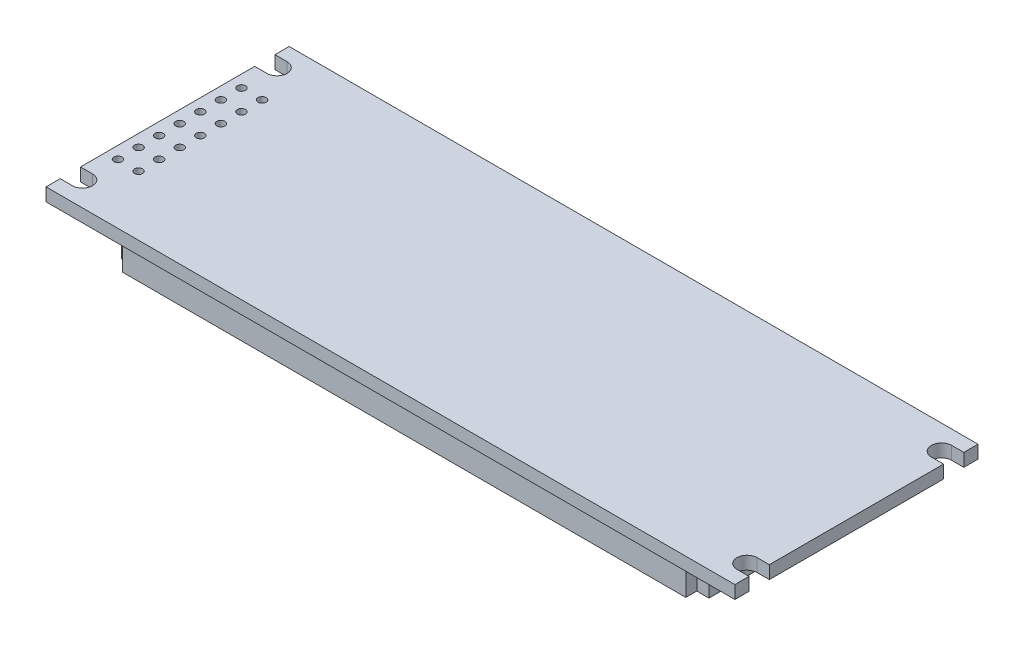
SolidWorks part; units mm, degrees
ref_plane "Plan de face" through (0, 0, 0) normal (0, 0, 1) x (1, 0, 0)
ref_plane "Plan de dessus" through (0, 0, 0) normal (0, 1, 0) x (1, 0, 0)
ref_plane "Plan de droite" through (0, 0, 0) normal (1, 0, 0) x (0, 0, -1)
sketch "Esquisse1" plane through (0, 0, 0) normal (0, 1, 0) x (1, 0, 0)
  line L0 (-41, -13.25) -> (-42.5, -13.25)
  line L1 (42.5, 15) -> (-42.5, 15)
  line L2 (-42.5, -10.75) -> (-42.5, 10.75)
  line L3 (42.5, -15) -> (-42.5, -15)
  line L4 (-42.5, -15) -> (-42.5, -13.25)
  line L5 (0, -15) -> (0, 15) construction
  line L6 (42.5, -15) -> (-42.5, 15) construction
  line L7 (-42.5, -10.75) -> (-41, -10.75)
  line L8 (-42.5, 0) -> (42.5, 0) construction
  line L10 (-42.5, 10.75) -> (-41, 10.75)
  line L11 (-42.5, 15) -> (-42.5, 13.25)
  line L12 (-41, 13.25) -> (-42.5, 13.25)
  line L13 (42.5, 15) -> (42.5, 13.25)
  line L14 (41, 13.25) -> (42.5, 13.25)
  line L15 (42.5, 10.75) -> (41, 10.75)
  line L16 (-42.5, 15) -> (42.5, -15) construction
  line L17 (42.5, -10.75) -> (41, -10.75)
  line L18 (42.5, -15) -> (42.5, -13.25)
  line L19 (41, -13.25) -> (42.5, -13.25)
  line L20 (42.5, -10.75) -> (42.5, 10.75)
  arc A0 (-41, -13.25) -> (-41, -10.75) centre (-41, -12) ccw
  arc A1 (-41, 13.25) -> (-41, 10.75) centre (-41, 12) cw
  arc A2 (41, 13.25) -> (41, 10.75) centre (41, 12) ccw
  arc A3 (41, -13.25) -> (41, -10.75) centre (41, -12) cw
  point P0 (0, 0)
  dimension "D1" = 85
  dimension "D3" = 82
  dimension "D5" = 1.25
  dimension "D2" = 30
  dimension "D4" = 24
extrude "Boss.-Extru.1" add sketch "Esquisse1" along normal blind 1.6
sketch "Esquisse2" plane through (0, 0, 0) normal (0, -1, 0) x (1, 0, 0)
  line L2 (42.5, 15) -> (-42.5, 15) construction
  line L3 (-42.5, 10.75) -> (-42.5, -10.75) construction
  circle A0 centre (-41, 7.62) radius 0.5
  circle A1 centre (-38.46, 7.62) radius 0.5
  circle A2 centre (-38.46, 5.08) radius 0.5
  circle A3 centre (-38.46, 2.54) radius 0.5
  circle A4 centre (-38.46, 0) radius 0.5
  circle A5 centre (-38.46, -2.54) radius 0.5
  circle A6 centre (-38.46, -5.08) radius 0.5
  circle A7 centre (-38.46, -7.62) radius 0.5
  circle A8 centre (-41, 5.08) radius 0.5
  circle A9 centre (-41, 2.54) radius 0.5
  circle A10 centre (-41, 0) radius 0.5
  circle A11 centre (-41, -2.54) radius 0.5
  circle A12 centre (-41, -5.08) radius 0.5
  circle A13 centre (-41, -7.62) radius 0.5
  dimension "D1" = 7.38
  dimension "D3" = 2
  dimension "D4" = 7
  dimension "D2" = 1.5
extrude "Enlèv. mat.-Extru.1" cut sketch "Esquisse2" against normal through all
sketch "Esquisse3" plane through (0, 0, 0) normal (0, -1, 0) x (1, 0, 0)
  line L0 (-34.75, 13.3) -> (-34.75, 11.95)
  line L1 (-34.75, 13.3) -> (34.75, 13.3)
  line L2 (36.25, 11.95) -> (36.25, -11.95)
  line L3 (34.75, -13.3) -> (-34.75, -13.3)
  line L4 (-36.25, -11.95) -> (-36.25, 11.95)
  line L7 (-34.75, 11.95) -> (-36.25, 11.95)
  line L11 (-34.75, -13.3) -> (-34.75, -11.95)
  line L12 (-34.75, -11.95) -> (-36.25, -11.95)
  line L13 (34.75, 13.3) -> (34.75, 11.95)
  line L14 (34.75, 11.95) -> (36.25, 11.95)
  line L15 (34.75, -11.95) -> (36.25, -11.95)
  line L16 (34.75, -13.3) -> (34.75, -11.95)
  point P0 (0, 0)
  point P1 (0, 0)
  point P7 (-36.25, 11.95)
  point P8 (-34.75, 13.3)
extrude "Boss.-Extru.2" add sketch "Esquisse3" along normal blind 4.5
sketch "Esquisse5" plane through (0, -4.5, 0) normal (0, -1, 0) x (1, 0, 0)
  line L1 (31, -8) -> (-31, -8)
  line L2 (31, -8) -> (31, 8)
  line L3 (31, 8) -> (-31, 8)
  line L4 (-31, -8) -> (-31, 8)
  line L5 (31, -8) -> (-31, 8) construction
  line L6 (31, 8) -> (-31, -8) construction
  point P0 (0, 0)
extrude "Enlèv. mat.-Extru.2" cut sketch "Esquisse5" against normal blind 0.2
sketch "Esquisse6" plane through (0, -4.3, 0) normal (0, -1, 0) x (1, 0, 0)
  line L1 (27.865, -5.49) -> (25.085, -5.49)
  line L2 (27.865, -5.49) -> (27.865, -0.6)
  line L3 (27.865, -0.6) -> (25.085, -0.6)
  line L4 (25.085, -5.49) -> (25.085, -0.6)
  line L5 (27.865, -5.49) -> (25.085, -0.6) construction
  line L6 (27.865, -0.6) -> (25.085, -5.49) construction
  line L7 (31, -8) -> (31, 8) construction
  line L8 (-31, -8) -> (31, -8) construction
  line L9 (24.385, -5.49) -> (21.605, -5.49)
  line L10 (24.385, -5.49) -> (24.385, -0.6)
  line L11 (24.385, -0.6) -> (21.605, -0.6)
  line L12 (21.605, -5.49) -> (21.605, -0.6)
  line L13 (20.905, -5.49) -> (18.125, -5.49)
  line L14 (20.905, -5.49) -> (20.905, -0.6)
  line L15 (20.905, -0.6) -> (18.125, -0.6)
  line L16 (18.125, -5.49) -> (18.125, -0.6)
  line L17 (17.425, -5.49) -> (14.645, -5.49)
  line L18 (17.425, -5.49) -> (17.425, -0.6)
  line L19 (17.425, -0.6) -> (14.645, -0.6)
  line L20 (14.645, -5.49) -> (14.645, -0.6)
  line L21 (13.945, -5.49) -> (11.165, -5.49)
  line L22 (13.945, -5.49) -> (13.945, -0.6)
  line L23 (13.945, -0.6) -> (11.165, -0.6)
  line L24 (11.165, -5.49) -> (11.165, -0.6)
  line L25 (10.465, -5.49) -> (7.685, -5.49)
  line L26 (10.465, -5.49) -> (10.465, -0.6)
  line L27 (10.465, -0.6) -> (7.685, -0.6)
  line L28 (7.685, -5.49) -> (7.685, -0.6)
  line L29 (6.985, -5.49) -> (4.205, -5.49)
  line L30 (6.985, -5.49) -> (6.985, -0.6)
  line L31 (6.985, -0.6) -> (4.205, -0.6)
  line L32 (4.205, -5.49) -> (4.205, -0.6)
  line L33 (3.505, -5.49) -> (0.725, -5.49)
  line L34 (3.505, -5.49) -> (3.505, -0.6)
  line L35 (3.505, -0.6) -> (0.725, -0.6)
  line L36 (0.725, -5.49) -> (0.725, -0.6)
  line L37 (0.025, -5.49) -> (-2.755, -5.49)
  line L38 (0.025, -5.49) -> (0.025, -0.6)
  line L39 (0.025, -0.6) -> (-2.755, -0.6)
  line L40 (-2.755, -5.49) -> (-2.755, -0.6)
  line L41 (-3.455, -5.49) -> (-6.235, -5.49)
  line L42 (-3.455, -5.49) -> (-3.455, -0.6)
  line L43 (-3.455, -0.6) -> (-6.235, -0.6)
  line L44 (-6.235, -5.49) -> (-6.235, -0.6)
  line L45 (-6.935, -5.49) -> (-9.715, -5.49)
  line L46 (-6.935, -5.49) -> (-6.935, -0.6)
  line L47 (-6.935, -0.6) -> (-9.715, -0.6)
  line L48 (-9.715, -5.49) -> (-9.715, -0.6)
  line L49 (-10.415, -5.49) -> (-13.195, -5.49)
  line L50 (-10.415, -5.49) -> (-10.415, -0.6)
  line L51 (-10.415, -0.6) -> (-13.195, -0.6)
  line L52 (-13.195, -5.49) -> (-13.195, -0.6)
  line L53 (-13.895, -5.49) -> (-16.675, -5.49)
  line L54 (-13.895, -5.49) -> (-13.895, -0.6)
  line L55 (-13.895, -0.6) -> (-16.675, -0.6)
  line L56 (-16.675, -5.49) -> (-16.675, -0.6)
  line L57 (-17.375, -5.49) -> (-20.155, -5.49)
  line L58 (-17.375, -5.49) -> (-17.375, -0.6)
  line L59 (-17.375, -0.6) -> (-20.155, -0.6)
  line L60 (-20.155, -5.49) -> (-20.155, -0.6)
  line L61 (-20.855, -5.49) -> (-23.635, -5.49)
  line L62 (-20.855, -5.49) -> (-20.855, -0.6)
  line L63 (-20.855, -0.6) -> (-23.635, -0.6)
  line L64 (-23.635, -5.49) -> (-23.635, -0.6)
  line L65 (-24.335, -5.49) -> (-27.115, -5.49)
  line L66 (-24.335, -5.49) -> (-24.335, -0.6)
  line L67 (-24.335, -0.6) -> (-27.115, -0.6)
  line L68 (-27.115, -5.49) -> (-27.115, -0.6)
  line L69 (27.865, 0.51) -> (25.085, 0.51)
  line L70 (27.865, 0.51) -> (27.865, 5.4)
  line L71 (27.865, 5.4) -> (25.085, 5.4)
  line L72 (25.085, 0.51) -> (25.085, 5.4)
  line L73 (24.385, 0.51) -> (21.605, 0.51)
  line L74 (24.385, 0.51) -> (24.385, 5.4)
  line L75 (24.385, 5.4) -> (21.605, 5.4)
  line L76 (21.605, 0.51) -> (21.605, 5.4)
  line L77 (20.905, 0.51) -> (18.125, 0.51)
  line L78 (20.905, 0.51) -> (20.905, 5.4)
  line L79 (20.905, 5.4) -> (18.125, 5.4)
  line L80 (18.125, 0.51) -> (18.125, 5.4)
  line L81 (17.425, 0.51) -> (14.645, 0.51)
  line L82 (17.425, 0.51) -> (17.425, 5.4)
  line L83 (17.425, 5.4) -> (14.645, 5.4)
  line L84 (14.645, 0.51) -> (14.645, 5.4)
  line L85 (13.945, 0.51) -> (11.165, 0.51)
  line L86 (13.945, 0.51) -> (13.945, 5.4)
  line L87 (13.945, 5.4) -> (11.165, 5.4)
  line L88 (11.165, 0.51) -> (11.165, 5.4)
  line L89 (10.465, 0.51) -> (7.685, 0.51)
  line L90 (10.465, 0.51) -> (10.465, 5.4)
  line L91 (10.465, 5.4) -> (7.685, 5.4)
  line L92 (7.685, 0.51) -> (7.685, 5.4)
  line L93 (6.985, 0.51) -> (4.205, 0.51)
  line L94 (6.985, 0.51) -> (6.985, 5.4)
  line L95 (6.985, 5.4) -> (4.205, 5.4)
  line L96 (4.205, 0.51) -> (4.205, 5.4)
  line L97 (3.505, 0.51) -> (0.725, 0.51)
  line L98 (3.505, 0.51) -> (3.505, 5.4)
  line L99 (3.505, 5.4) -> (0.725, 5.4)
  line L100 (0.725, 0.51) -> (0.725, 5.4)
  line L101 (0.025, 0.51) -> (-2.755, 0.51)
  line L102 (0.025, 0.51) -> (0.025, 5.4)
  line L103 (0.025, 5.4) -> (-2.755, 5.4)
  line L104 (-2.755, 0.51) -> (-2.755, 5.4)
  line L105 (-3.455, 0.51) -> (-6.235, 0.51)
  line L106 (-3.455, 0.51) -> (-3.455, 5.4)
  line L107 (-3.455, 5.4) -> (-6.235, 5.4)
  line L108 (-6.235, 0.51) -> (-6.235, 5.4)
  line L109 (-6.935, 0.51) -> (-9.715, 0.51)
  line L110 (-6.935, 0.51) -> (-6.935, 5.4)
  line L111 (-6.935, 5.4) -> (-9.715, 5.4)
  line L112 (-9.715, 0.51) -> (-9.715, 5.4)
  line L113 (-10.415, 0.51) -> (-13.195, 0.51)
  line L114 (-10.415, 0.51) -> (-10.415, 5.4)
  line L115 (-10.415, 5.4) -> (-13.195, 5.4)
  line L116 (-13.195, 0.51) -> (-13.195, 5.4)
  line L117 (-13.895, 0.51) -> (-16.675, 0.51)
  line L118 (-13.895, 0.51) -> (-13.895, 5.4)
  line L119 (-13.895, 5.4) -> (-16.675, 5.4)
  line L120 (-16.675, 0.51) -> (-16.675, 5.4)
  line L121 (-17.375, 0.51) -> (-20.155, 0.51)
  line L122 (-17.375, 0.51) -> (-17.375, 5.4)
  line L123 (-17.375, 5.4) -> (-20.155, 5.4)
  line L124 (-20.155, 0.51) -> (-20.155, 5.4)
  line L125 (-20.855, 0.51) -> (-23.635, 0.51)
  line L126 (-20.855, 0.51) -> (-20.855, 5.4)
  line L127 (-20.855, 5.4) -> (-23.635, 5.4)
  line L128 (-23.635, 0.51) -> (-23.635, 5.4)
  line L129 (-24.335, 0.51) -> (-27.115, 0.51)
  line L130 (-24.335, 0.51) -> (-24.335, 5.4)
  line L131 (-24.335, 5.4) -> (-27.115, 5.4)
  line L132 (-27.115, 0.51) -> (-27.115, 5.4)
  point P0 (26.475, -3.045)
  dimension "D1" = 3.135
  dimension "D2" = 2.51
  dimension "D3" = 16
  dimension "D4" = 2
extrude "Enlèv. mat.-Extru.3" cut sketch "Esquisse6" against normal blind 0.1
